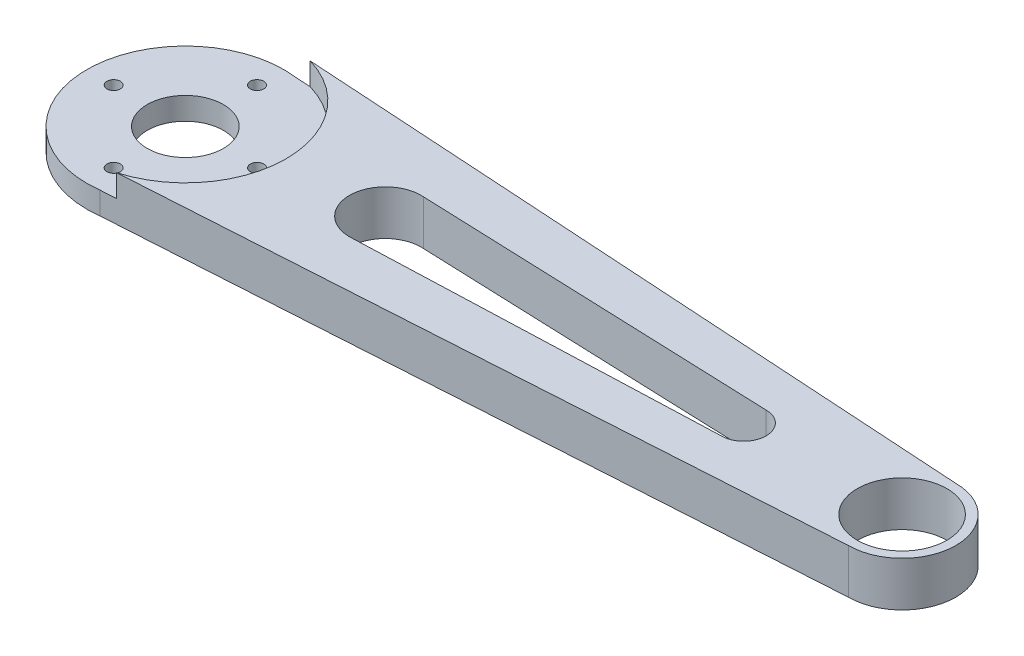
SolidWorks part; units mm, degrees
ref_plane "Front" through (0, 0, 0) normal (0, 0, 1) x (1, 0, 0)
ref_plane "Top" through (0, 0, 0) normal (0, 1, 0) x (1, 0, 0)
ref_plane "Right" through (0, 0, 0) normal (1, 0, 0) x (0, 0, -1)
sketch "草图1" plane through (0, 0, 0) normal (0, 1, 0) x (1, 0, 0)
  line L0 (-59.0043, 0) -> (63.069, 0) construction
  circle A0 centre (-44.3188, 0) radius 11
  circle A1 centre (35.6812, 0) radius 6
  dimension "D1" = 22
  dimension "D3" = 12
  dimension "D2" = 80
extrude "凸台-拉伸1" add sketch "草图1" along normal blind 5
sketch "草图3" plane through (0, 0, 0) normal (0, 1, 0) x (1, 0, 0)
  line L0 (-61.778, 0) -> (78.4405, 0) construction
  line L1 (0, 36.4306) -> (0, -33.6787) construction
  line L2 (-44.3188, 11) -> (35.6812, 6)
  line L3 (35.6812, 6) -> (35.6812, -6)
  line L4 (35.6812, -6) -> (-44.3188, -11)
  line L5 (-44.3188, -11) -> (-44.3188, 11)
  circle A0 centre (-44.3188, 0) radius 11 construction
  circle A1 centre (35.6812, 0) radius 6 construction
extrude "凸台-拉伸3" add sketch "草图3" along normal blind 5
sketch "草图4" plane through (0, 5, 0) normal (0, 1, 0) x (1, 0, 0)
  circle A0 centre (-44.3188, 0) radius 11.25
  dimension "D1" = 22.5
extrude "切除-拉伸1" cut sketch "草图4" against normal blind 2.5
sketch "草图5" plane through (0, 5, 0) normal (0, 1, 0) x (1, 0, 0)
  circle A0 centre (35.6812, 0) radius 5
  dimension "D1" = 10
extrude "切除-拉伸2" cut sketch "草图5" against normal through all
sketch "草图6" plane through (0, 5, 0) normal (0, 1, 0) x (1, 0, 0)
  line L0 (-65.6937, 0) -> (69.5957, 0) construction
  circle A2 centre (-22, 0) radius 4
  circle A3 centre (18, 0) radius 2.5
  dimension "D3" = 8
  dimension "D4" = 5
  dimension "D1" = 22
  dimension "D2" = 18
extrude "切除-拉伸3" cut sketch "草图6" against normal through all
sketch "草图7" plane through (0, 5, 0) normal (0, 1, 0) x (1, 0, 0)
  line L0 (-22, 4) -> (18, 2.5)
  line L1 (18, 2.5) -> (18, -2.5)
  line L2 (18, -2.5) -> (-22, -4)
  line L3 (-22, -4) -> (-22, 4)
  circle A0 centre (-22, 0) radius 4 construction
  circle A1 centre (18, 0) radius 2.5 construction
extrude "切除-拉伸4" cut sketch "草图7" against normal through all
sketch "草图8" plane through (0, 2.5, 0) normal (0, 1, 0) x (1, 0, 0)
  line L0 (-63.8785, 0) -> (-31.3175, 0) construction
  line L1 (-44.3188, 0) -> (-44.3188, 24.2559) construction
  circle A1 centre (-52.3188, 0) radius 0.7477
  circle A4 centre (-36.3188, 0) radius 0.7477
  circle A6 centre (-44.3188, 8) radius 0.75
  circle A7 centre (-44.3188, -8) radius 0.75
  dimension "D1" = 1.5
  dimension "D2" = 16
  dimension "D4" = 16
extrude "切除-拉伸5" cut sketch "草图8" against normal through all
sketch "草图9" plane through (0, 2.5, 0) normal (0, 1, 0) x (1, 0, 0)
  circle A0 centre (-44.3188, 0) radius 4.25
  dimension "D1" = 8.5
extrude "切除-拉伸6" cut sketch "草图9" against normal through all
